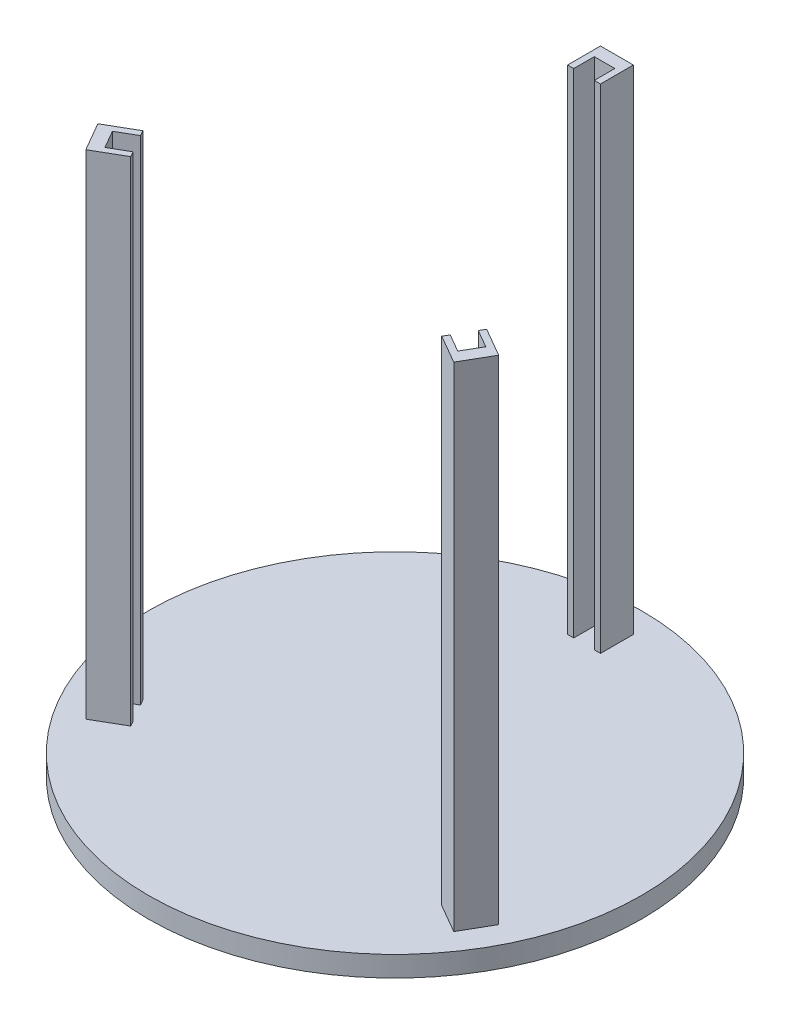
SolidWorks part; units mm, degrees
ref_plane "Front Plane" through (0, 0, 0) normal (0, 0, 1) x (1, 0, 0)
ref_plane "Top Plane" through (0, 0, 0) normal (0, 1, 0) x (1, 0, 0)
ref_plane "Right Plane" through (0, 0, 0) normal (1, 0, 0) x (0, 0, -1)
sketch "Sketch2" plane through (0, 0, 0) normal (0, 1, 0) x (1, 0, 0)
  circle A0 centre (0, 0) radius 300
  dimension "D1" = 600
extrude "Boss-Extrude1" add sketch "Sketch2" along normal blind 25
sketch "Sketch3" plane through (0, 25, 0) normal (0, 1, 0) x (1, 0, 0)
  circle A0 centre (0, 99.0898) radius 9.3435
extrude "Cut-Extrude1" [suppressed] cut sketch "Sketch3" against normal through all
pattern_circular "CirPattern1" [suppressed] count 3 over 360
sketch "Sketch4" plane through (0, 25, 0) normal (0, 1, 0) x (1, 0, 0)
  line L1 (-20, 230) -> (20, 230)
  line L2 (-20, 230) -> (-20, 270)
  line L3 (-20, 270) -> (20, 270)
  line L4 (20, 230) -> (20, 270)
  line L5 (-20, 230) -> (20, 270) construction
  line L6 (-20, 270) -> (20, 230) construction
  point P0 (0, 250)
  dimension "D1" = 40
  dimension "D2" = 40
  dimension "D3" = 250
extrude "Boss-Extrude2" add sketch "Sketch4" along normal blind 600
sketch "Sketch5" plane through (0, 625, 0) normal (0, 1, 0) x (1, 0, 0)
  line L0 (-12.5429, 230) -> (-12.5429, 255)
  line L1 (-20, 230) -> (20, 230) construction
  line L2 (-12.5429, 255) -> (12.4571, 255)
  line L3 (12.4571, 255) -> (12.4571, 230)
  line L4 (12.4571, 230) -> (-12.5429, 230)
  line L5 (-0.0429, 255) -> (-0.0429, 230) construction
  dimension "D1" = 25
  dimension "D2" = 25
extrude "Cut-Extrude3" cut sketch "Sketch5" against normal blind 600
pattern_circular "CirPattern2" count 3 over 360 about axis through (0, 0, 0) along (0, 1, 0) of "Cut-Extrude3", "Boss-Extrude2"
